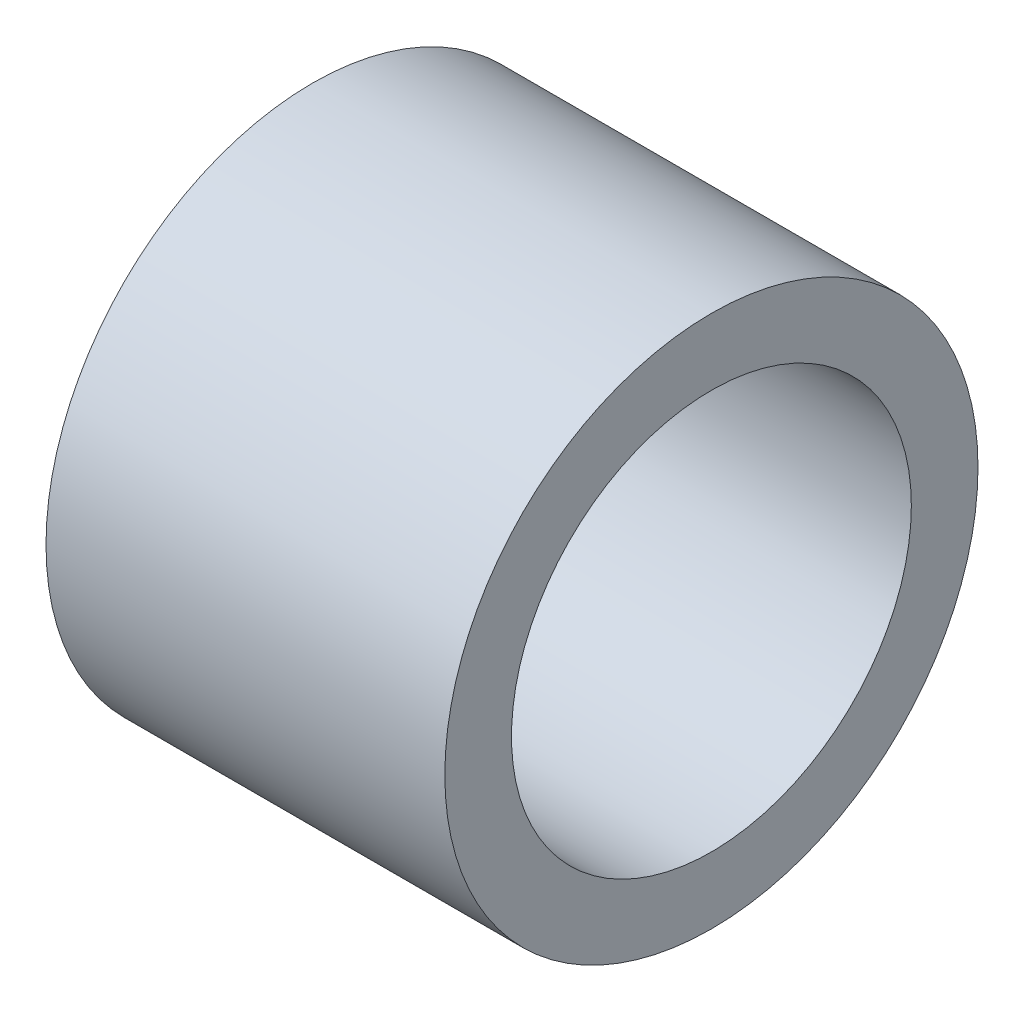
SolidWorks part; units mm, degrees
ref_plane "Front Plane" through (0, 0, 0) normal (0, 0, 1) x (1, 0, 0)
ref_plane "Top Plane" through (0, 0, 0) normal (0, 1, 0) x (1, 0, 0)
ref_plane "Right Plane" through (0, 0, 0) normal (1, 0, 0) x (0, 0, -1)
sketch "Sketch1" plane through (0, 0, 0) normal (1, 0, 0) x (0, 0, -1)
  circle A0 centre (0, 0) radius 12.7
  circle A1 centre (0, 0) radius 9.525
  dimension "D1" = 25.4
  dimension "D2" = 19.05
extrude "Boss-Extrude1" add sketch "Sketch1" along normal mid plane 19
